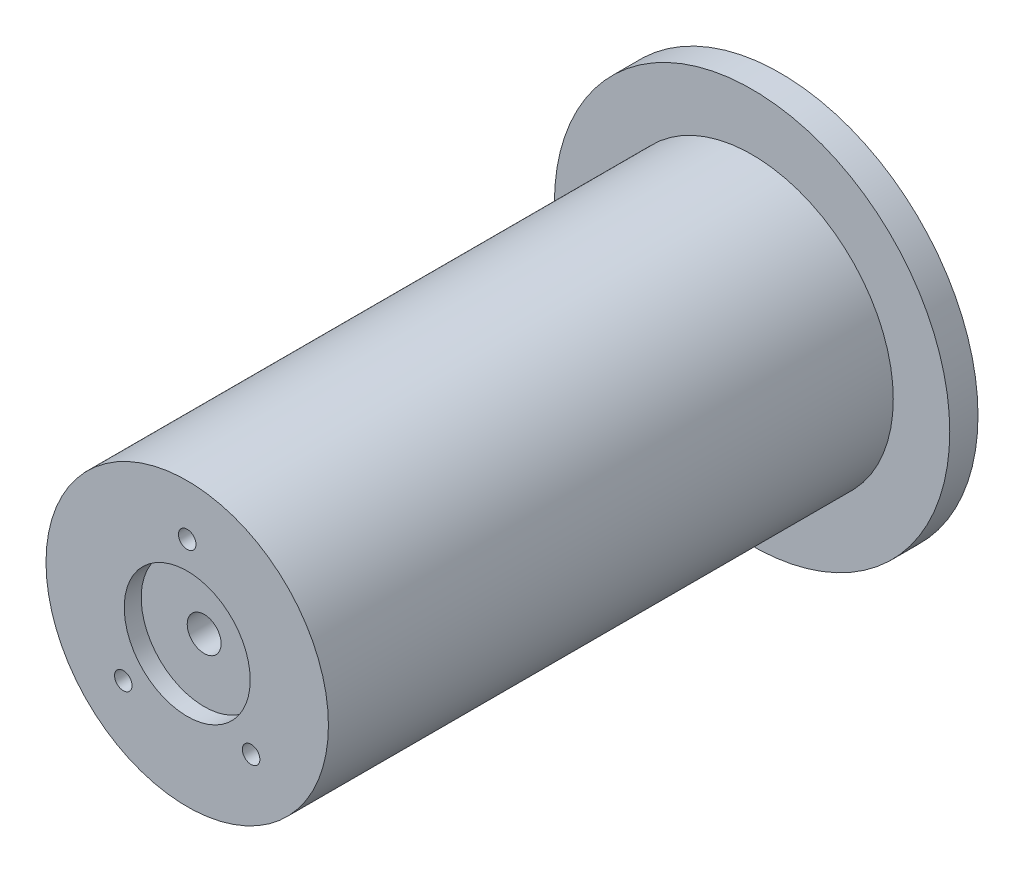
SolidWorks part; units mm, degrees
ref_plane "Спереди" through (0, 0, 0) normal (0, 0, 1) x (1, 0, 0)
ref_plane "Сверху" through (0, 0, 0) normal (0, 1, 0) x (1, 0, 0)
ref_plane "Справа" through (0, 0, 0) normal (1, 0, 0) x (0, 0, -1)
sketch "Эскиз1" plane through (0, 0, 0) normal (0, 0, 1) x (1, 0, 0)
  circle A0 centre (0, 0) radius 25
  dimension "D1" = 50
extrude "Бобышка-Вытянуть1" add sketch "Эскиз1" along normal blind 100
sketch "Эскиз2" plane through (0, 0, 0) normal (0, 0, -1) x (-1, 0, 0)
  circle A0 centre (0, 0) radius 35
  dimension "D1" = 70
extrude "Бобышка-Вытянуть2" add sketch "Эскиз2" along normal blind 5
sketch "Эскиз4" plane through (0, 0, -5) normal (0, 0, -1) x (-1, 0, 0)
  circle A0 centre (0, 0) radius 9.8
  dimension "D1" = 19.6
extrude "Вырез-Вытянуть1" cut sketch "Эскиз4" against normal blind 7
sketch "Эскиз5" plane through (0, 0, -5) normal (0, 0, -1) x (-1, 0, 0)
  circle A0 centre (0, 0) radius 3
  dimension "D1" = 6
extrude "Вырез-Вытянуть2" cut sketch "Эскиз5" against normal through all
sketch "Эскиз6" plane through (0, 0, -5) normal (0, 0, -1) x (-1, 0, 0)
  line L0 (0, 13) -> (11.2583, -6.5) construction
  line L1 (11.2583, -6.5) -> (-11.2583, -6.5) construction
  line L2 (-11.2583, -6.5) -> (0, 13) construction
  circle A0 centre (0, 0) radius 13 construction
  circle A1 centre (0, 13) radius 1.5
  circle A2 centre (11.2583, -6.5) radius 1.5
  circle A3 centre (-11.2583, -6.5) radius 1.5
  dimension "D1" = 26
  dimension "D2" = 3
extrude "Вырез-Вытянуть3" cut sketch "Эскиз6" against normal blind 10
sketch "Эскиз7" plane through (0, 0, 100) normal (0, 0, 1) x (1, 0, 0)
  circle A0 centre (0, 0) radius 11.15
  dimension "D1" = 22.3
extrude "Вырез-Вытянуть4" cut sketch "Эскиз7" against normal blind 3
sketch "Эскиз8" plane through (0, 0, 100) normal (0, 0, 1) x (1, 0, 0)
  line L0 (0, 0) -> (-11.3137, -11.3137) construction
  line L1 (0, 0) -> (0, -53.0175) construction
  circle A0 centre (0, 0) radius 16 construction
  circle A1 centre (0, 16) radius 1.55
  circle A2 centre (-11.3137, -11.3137) radius 1.55
  circle A3 centre (11.3137, -11.3137) radius 1.55
  dimension "D1" = 32
  dimension "D2" = 3.1
  dimension "D3" = 45
extrude "Вырез-Вытянуть5" cut sketch "Эскиз8" against normal blind 10
